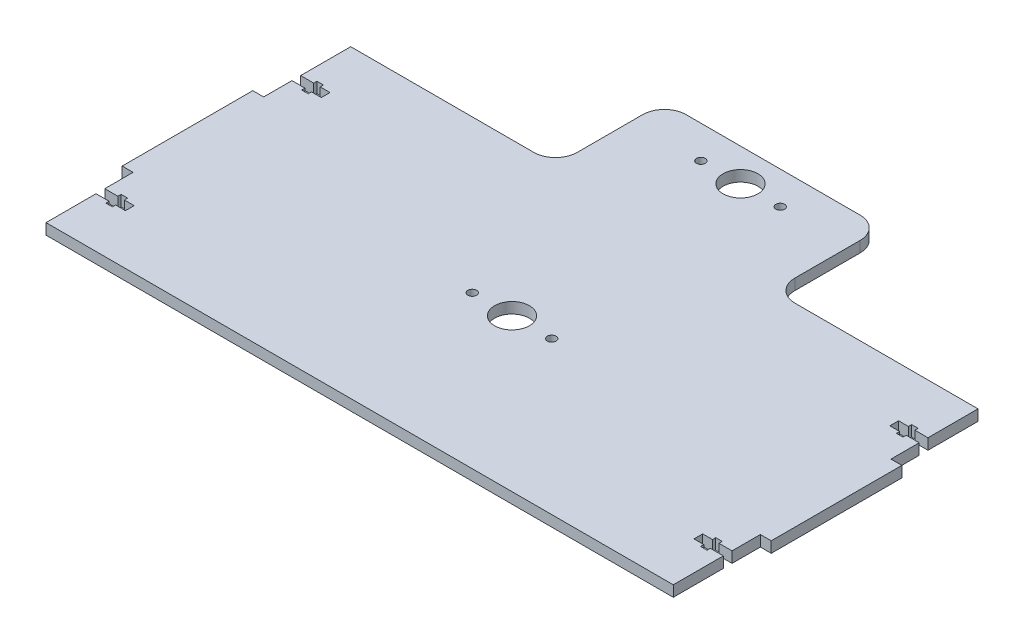
SolidWorks part; units mm, degrees
ref_plane "Front Plane" through (0, 0, 0) normal (0, 0, 1) x (1, 0, 0)
ref_plane "Top Plane" through (0, 0, 0) normal (0, 1, 0) x (1, 0, 0)
ref_plane "Right Plane" through (0, 0, 0) normal (1, 0, 0) x (0, 0, -1)
sketch "Sketch1" plane through (0, 0, 0) normal (0, 1, 0) x (1, 0, 0)
  line L1 (144.1, -70) -> (-144.1, -70)
  line L2 (144.1, -70) -> (144.1, 70)
  line L3 (144.1, 70) -> (-144.1, 70)
  line L4 (-144.1, -70) -> (-144.1, 70)
  line L5 (144.1, -70) -> (-144.1, 70) construction
  line L6 (144.1, 70) -> (-144.1, -70) construction
  point P0 (0, 0)
  dimension "D1" = 288.2
  dimension "D2" = 140
extrude "5" add sketch "Sketch1" along normal blind 5
sketch "Sketch2" plane through (0, 5, 0) normal (0, 1, 0) x (1, 0, 0)
  line L0 (144.1, -70) -> (144.1, 70) construction
  line L1 (139.1, -30) -> (149.1, -30)
  line L2 (139.1, -30) -> (139.1, 30)
  line L3 (139.1, 30) -> (149.1, 30)
  line L4 (149.1, -30) -> (149.1, 30)
  line L5 (139.1, -30) -> (149.1, 30) construction
  line L6 (139.1, 30) -> (149.1, -30) construction
  point P0 (144.1, 0)
  dimension "D1" = 10
  dimension "D2" = 60
extrude "Boss-Extrude2" add sketch "Sketch2" against normal blind 5
mirror "Mirror1" about plane through (0, 0, 0) normal (1, 0, 0) of "Boss-Extrude2"
sketch "Sketch3" plane through (0, 5, 0) normal (0, 1, 0) x (1, 0, 0)
  line L0 (144.1, 30) -> (144.1, 70) construction
  line L1 (157.6, 43) -> (130.6, 43)
  line L2 (157.6, 43) -> (157.6, 47)
  line L3 (157.6, 47) -> (130.6, 47)
  line L4 (130.6, 43) -> (130.6, 47)
  line L5 (157.6, 43) -> (130.6, 47) construction
  line L6 (157.6, 47) -> (130.6, 43) construction
  line L7 (149.1, -30) -> (149.1, 30) construction
  line L8 (-55, 0) -> (55, 0) construction
  line L9 (138.1, 41.5) -> (135.1, 41.5)
  line L10 (138.1, 41.5) -> (138.1, 48.5)
  line L11 (138.1, 48.5) -> (135.1, 48.5)
  line L12 (135.1, 41.5) -> (135.1, 48.5)
  line L13 (138.1, 41.5) -> (135.1, 48.5) construction
  line L14 (138.1, 48.5) -> (135.1, 41.5) construction
  line L15 (138.1, -48.5) -> (135.1, -41.5) construction
  line L16 (138.1, -41.5) -> (135.1, -48.5) construction
  line L17 (157.6, -47) -> (130.6, -43) construction
  line L18 (157.6, -43) -> (130.6, -47) construction
  line L19 (135.1, -41.5) -> (135.1, -48.5)
  line L20 (138.1, -48.5) -> (135.1, -48.5)
  line L21 (138.1, -41.5) -> (138.1, -48.5)
  line L22 (138.1, -41.5) -> (135.1, -41.5)
  line L23 (130.6, -43) -> (130.6, -47)
  line L24 (157.6, -47) -> (130.6, -47)
  line L25 (157.6, -43) -> (157.6, -47)
  line L26 (157.6, -43) -> (130.6, -43)
  line L27 (0, -55) -> (0, 55) construction
  line L28 (-157.6, -43) -> (-130.6, -47) construction
  line L29 (-157.6, -47) -> (-130.6, -43) construction
  line L30 (-138.1, -41.5) -> (-135.1, -48.5) construction
  line L31 (-138.1, -48.5) -> (-135.1, -41.5) construction
  line L32 (-138.1, 48.5) -> (-135.1, 41.5) construction
  line L33 (-138.1, 41.5) -> (-135.1, 48.5) construction
  line L34 (-157.6, 47) -> (-130.6, 43) construction
  line L35 (-157.6, 43) -> (-130.6, 47) construction
  line L36 (-157.6, -43) -> (-130.6, -43)
  line L37 (-157.6, -43) -> (-157.6, -47)
  line L38 (-157.6, -47) -> (-130.6, -47)
  line L39 (-130.6, -43) -> (-130.6, -47)
  line L40 (-138.1, -41.5) -> (-135.1, -41.5)
  line L41 (-138.1, -41.5) -> (-138.1, -48.5)
  line L42 (-138.1, -48.5) -> (-135.1, -48.5)
  line L43 (-135.1, -41.5) -> (-135.1, -48.5)
  line L44 (-135.1, 41.5) -> (-135.1, 48.5)
  line L45 (-138.1, 48.5) -> (-135.1, 48.5)
  line L46 (-138.1, 41.5) -> (-138.1, 48.5)
  line L47 (-138.1, 41.5) -> (-135.1, 41.5)
  line L48 (-130.6, 43) -> (-130.6, 47)
  line L49 (-157.6, 47) -> (-130.6, 47)
  line L50 (-157.6, 43) -> (-157.6, 47)
  line L51 (-157.6, 43) -> (-130.6, 43)
  point P0 (144.1, 45)
  point P9 (149.1, 0)
  point P10 (136.6, 45)
  point P25 (136.6, -45)
  point P26 (144.1, -45)
  point P45 (-144.1, -45)
  point P46 (-136.6, -45)
  point P47 (-136.6, 45)
  point P48 (-144.1, 45)
  dimension "D1" = 4
  dimension "D2" = 45
  dimension "D3" = 27
  dimension "D4" = 3
  dimension "D5" = 7
  dimension "D6" = 0
  dimension "D7" = 7.5
extrude "Cut-Extrude1" cut sketch "Sketch3" against normal blind 5 contours L49 L48 L51 L50 | L45 L44 L47 L46 | L36 L39 L38 L37 | L43 L42 L41 L40 | L3 L4 L1 L2 | L10 L11 L12 L9 | L21 L20 L19 L22 | L26 L23 L24 L25
sketch "Sketch4" plane through (0, 5, 0) normal (0, 1, 0) x (1, 0, 0)
  circle A0 centre (0, 0) radius 8
extrude "Cut-Extrude2" cut sketch "Sketch4" against normal blind 5
sketch "Sketch5" plane through (0, 5, 0) normal (0, 1, 0) x (1, 0, 0)
  line L0 (0, -2.75) -> (0, 2.75) construction
  circle A0 centre (-18.25, 0) radius 2
  circle A1 centre (0, 0) radius 8 construction
  circle A2 centre (18.25, 0) radius 2
  dimension "D1" = 18.25
extrude "Cut-Extrude3" cut sketch "Sketch5" against normal blind 5
sketch "Sketch6" plane through (0, 5, 0) normal (0, 1, 0) x (1, 0, 0)
  line L0 (144.1, 70) -> (-144.1, 70) construction
  line L1 (-50, 70) -> (50, 70)
  line L2 (0, 70) -> (0, 120)
  line L3 (-50, 120) -> (50, 120)
  line L4 (50, 70) -> (50, 120)
  line L5 (0, -2.75) -> (0, 2.75) construction
  line L6 (-50, 70) -> (-50, 120)
  dimension "D1" = 50
  dimension "D2" = 50
extrude "Boss-Extrude3" add sketch "Sketch6" against normal blind 5 contours L6 L1 L2 L3 | L1 L4 L3 L2
pattern_linear "LPattern1" count 2 spacing 105 along (0, 0, -1) of "Cut-Extrude3", "Cut-Extrude2"
fillet "Fillet1" radius 10 2 edges at (50, 2.5, -70) (-50, 2.5, -70)
fillet "Fillet2" radius 10 2 edges at (50, 2.5, -120) (-50, 2.5, -120)
